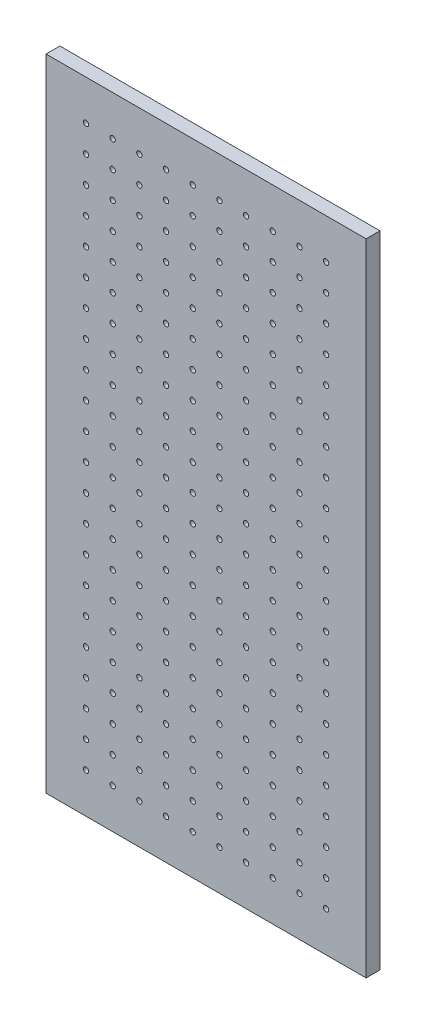
SolidWorks part; units mm, degrees
ref_plane "前视基准面" through (0, 0, 0) normal (0, 0, 1) x (1, 0, 0)
ref_plane "上视基准面" through (0, 0, 0) normal (0, 1, 0) x (1, 0, 0)
ref_plane "右视基准面" through (0, 0, 0) normal (1, 0, 0) x (0, 0, -1)
sketch "草图1" plane through (0, 0, 0) normal (0, 0, 1) x (1, 0, 0)
  line L1 (-150, 300) -> (150, 300)
  line L2 (-150, 300) -> (-150, -300)
  line L3 (-150, -300) -> (150, -300)
  line L4 (150, 300) -> (150, -300)
  line L5 (-150, 300) -> (150, -300) construction
  line L6 (-150, -300) -> (150, 300) construction
  point P0 (0, 0)
  dimension "D1" = 300
  dimension "D2" = 600
extrude "凸台-拉伸1" add sketch "草图1" along normal blind 13
sketch "草图2" plane through (0, 0, 13) normal (0, 0, 1) x (1, 0, 0)
  line L0 (150, 300) -> (-150, 300) construction
  line L1 (-112.5, 262.5) -> (112.5, 262.5) construction
  line L2 (-112.5, 262.5) -> (-112.5, -262.5) construction
  line L3 (-112.5, -262.5) -> (112.5, -262.5) construction
  line L4 (112.5, 262.5) -> (112.5, -262.5) construction
  line L5 (-112.5, 262.5) -> (112.5, -262.5) construction
  line L6 (-112.5, -262.5) -> (112.5, 262.5) construction
  line L7 (150, -300) -> (150, 300) construction
  point P0 (0, 0)
  dimension "D1" = 37.5
  dimension "D2" = 37.5
hole_wizard "M6 螺纹孔的螺纹孔钻头1" positions "草图3" profile "草图4" hole size "M6" standard "DIN" end condition through all
sketch "草图3" plane through (0, 0, 13) normal (0, 0, 1) x (1, 0, 0)
  point P0 (-112.5, -262.5)
sketch "草图4" plane through (-112.5, -262.5, 13) normal (1, 0, 0) x (0, -1, 0)
  line L0 (0, 0) -> (0, 13)
  line L1 (0, 13) -> (2.5, 13)
  line L2 (2.5, 13) -> (2.5, 0)
  line L5 (2.5, 0) -> (0, 0)
  line L11 (0, -6.35) -> (0, 107.95) construction
  dimension "通孔孔直径" = 5
  dimension "通孔孔深度" = 13
pattern_linear "阵列(线性)1" count 22 spacing 25 along (0, 1, 0) count 10 spacing 25 along (1, 0, 0) of "M6 螺纹孔的螺纹孔钻头1"
